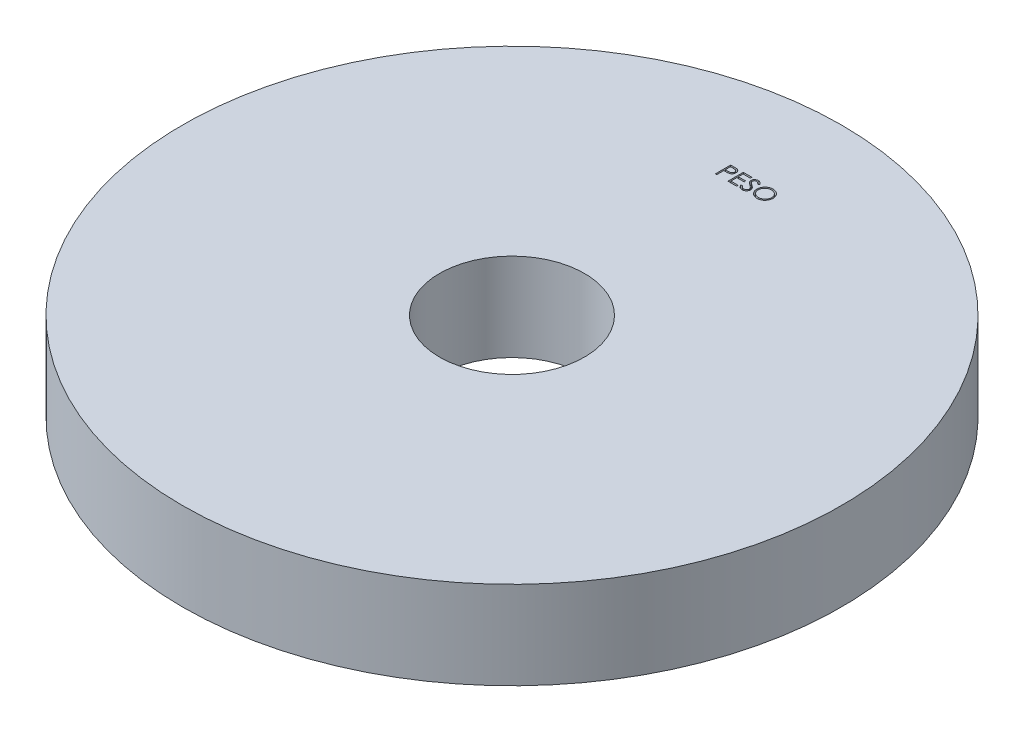
SolidWorks part; units mm, degrees
ref_plane "Plano frontal" through (0, 0, 0) normal (0, 0, 1) x (1, 0, 0)
ref_plane "Plano superior" through (0, 0, 0) normal (0, 1, 0) x (1, 0, 0)
ref_plane "Plano direito" through (0, 0, 0) normal (1, 0, 0) x (0, 0, -1)
sketch "Esboço1" plane through (0, 0, 0) normal (0, 1, 0) x (1, 0, 0)
  circle A0 centre (0, 0) radius 75
  circle A1 centre (0, 0) radius 16.5
  dimension "D1" = 33
  dimension "D2" = 150
extrude "Ressalto-extrusão1" add sketch "Esboço1" along normal blind 20
sketch "Esboço2" plane through (0, 20, 0) normal (0, 1, 0) x (1, 0, 0)
  text T0 "PESO"
extrude "Corte-extrusão1" cut sketch "Esboço2" against normal blind 1
